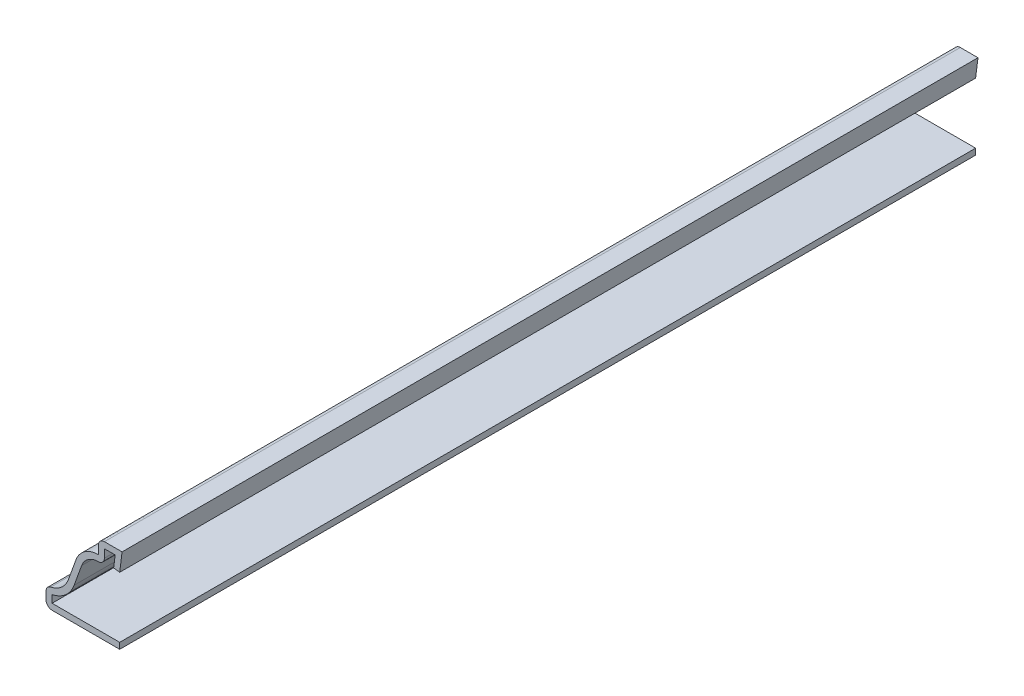
SolidWorks part; units mm, degrees
ref_plane "Front Plane" through (0, 0, 0) normal (0, 0, 1) x (1, 0, 0)
ref_plane "Top Plane" through (0, 0, 0) normal (0, 1, 0) x (1, 0, 0)
ref_plane "Right Plane" through (0, 0, 0) normal (1, 0, 0) x (0, 0, -1)
sketch "Sketch1" plane through (0, 0, 0) normal (0, 0, 1) x (1, 0, 0)
  line L0 (-0.3969, 0) -> (-12.7, 0)
  line L1 (-12.7, 0) -> (-12.7, 3.175)
  line L2 (-8.969, 5.7906) -> (-7.6997, 9.2906)
  line L3 (-3.9688, 11.9062) -> (-3.9688, 14.2875)
  line L4 (-3.9688, 14.2875) -> (0, 14.2875)
  line L5 (0, 14.2875) -> (-0.3969, 11.1374)
  arc A0 (-12.7, 3.175) -> (-8.969, 5.7906) centre (-12.7, 7.1437) ccw
  arc A1 (-7.6997, 9.2906) -> (-3.9688, 11.9062) centre (-3.9688, 7.9375) cw
  point P9 (0, 0)
  point P13 (-9.4457, 6.1705)
  point P14 (-7.4286, 10.1469)
  point P15 (0, 0)
  point P16 (0, 0)
  dimension "D9" = 3.9688
  dimension "D10" = 3.9688
  dimension "D1" = 12.7
  dimension "D2" = 3.9688
  dimension "D3" = 3.175
  dimension "D4" = 2.3813
  dimension "D5" = 3.175
  dimension "D6" = 14.2875
  dimension "D7" = 12.3031
  dimension "D8" = 0.3969
extrude "Extrude-Thin1" add sketch "Sketch1" against normal blind 142.875 thin
fillet "Fillet1" radius 1.016 4 edges at (-12.7, 0, -71.4375) (-12.7, 3.175, -71.4375) (-2.9527, 10.7099, -71.4375) (-3.9688, 14.2875, -71.4375)
